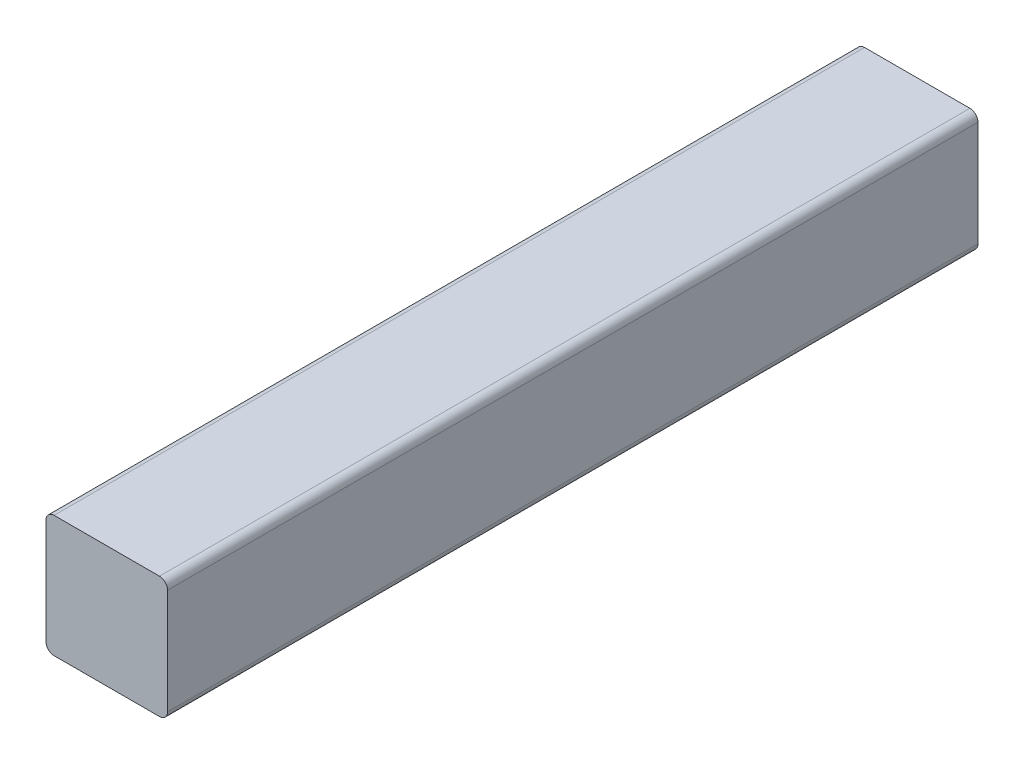
SolidWorks part; units mm, degrees
ref_plane "Front Plane" through (0, 0, 0) normal (0, 0, 1) x (1, 0, 0)
ref_plane "Top Plane" through (0, 0, 0) normal (0, 1, 0) x (1, 0, 0)
ref_plane "Right Plane" through (0, 0, 0) normal (1, 0, 0) x (0, 0, -1)
sketch "Sketch1" plane through (0, 0, 0) normal (0, 0, 1) x (1, 0, 0)
  line L0 (2, 0) -> (28, 0)
  line L1 (30, 2) -> (30, 28)
  line L2 (28, 30) -> (2, 30)
  line L3 (0, 28) -> (0, 2)
  arc A0 (2, 0) -> (0, 2) centre (2, 2) cw
  arc A1 (30, 2) -> (28, 0) centre (28, 2) cw
  arc A2 (28, 30) -> (30, 28) centre (28, 28) cw
  arc A3 (0, 28) -> (2, 30) centre (2, 28) cw
  point P7 (0, 0)
  dimension "D1" = 2
  dimension "D2" = 2
  dimension "D3" = 2
  dimension "D4" = 2
sketch "Sketch3" plane through (0, 0, 0) normal (0, 0, 1) x (1, 0, 0)
  line L0 (2, 0) -> (28, 0)
  line L1 (30, 2) -> (30, 28)
  line L2 (28, 30) -> (2, 30)
  line L3 (0, 28) -> (0, 2)
  arc A0 (2, 0) -> (0, 2) centre (2, 2) cw
  arc A1 (30, 2) -> (28, 0) centre (28, 2) cw
  arc A2 (28, 30) -> (30, 28) centre (28, 28) cw
  arc A3 (0, 28) -> (2, 30) centre (2, 28) cw
  dimension "D1" = 2
extrude "Boss-Extrude1" add sketch "Sketch3" along normal blind 200
